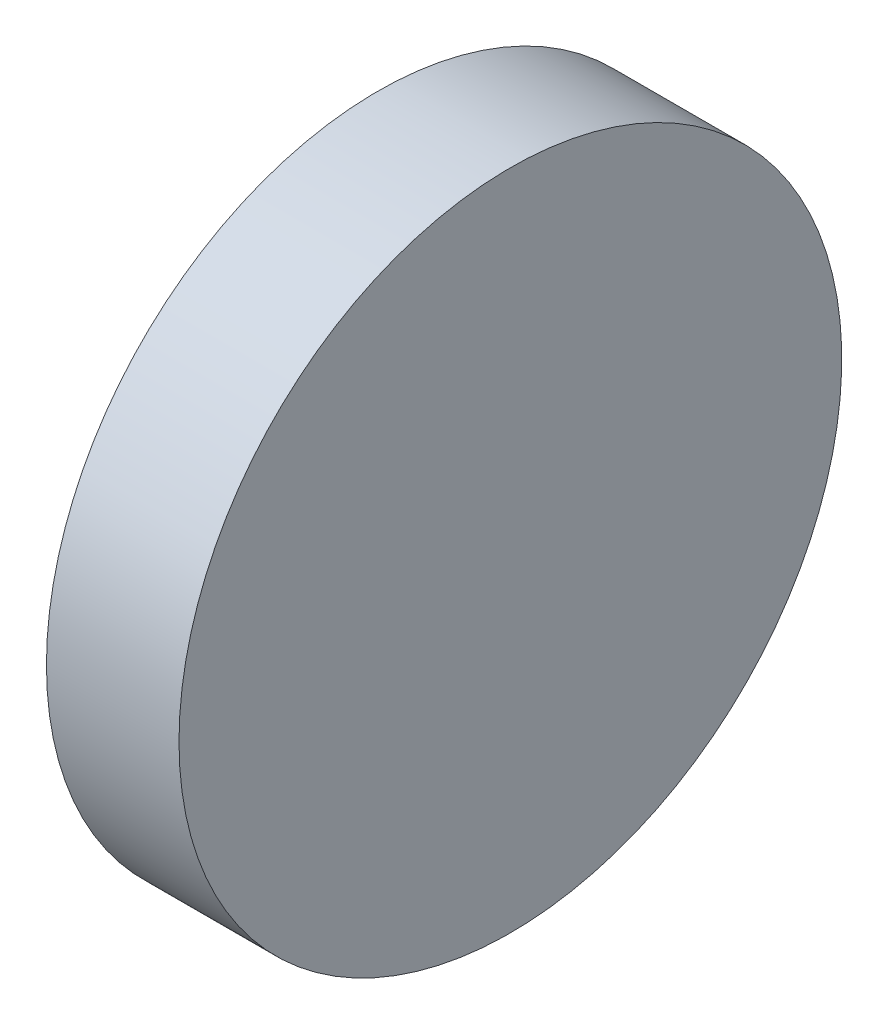
SolidWorks part; units mm, degrees
ref_plane "前视基准面" through (0, 0, 0) normal (0, 0, 1) x (1, 0, 0)
ref_plane "上视基准面" through (0, 0, 0) normal (0, 1, 0) x (1, 0, 0)
ref_plane "右视基准面" through (0, 0, 0) normal (1, 0, 0) x (0, 0, -1)
sketch "草图1" plane through (0, 0, 0) normal (0, 0, 1) x (1, 0, 0)
  line L0 (508.0016, 154.5864) -> (542.9445, 154.5864) construction
  line L1 (520.3143, 154.5864) -> (520.3143, 179.5864)
  line L2 (530.3143, 154.5864) -> (530.3143, 179.5864)
  line L3 (520.3143, 154.5864) -> (530.3143, 154.5864)
  line L5 (520.3143, 179.5864) -> (530.3143, 179.5864)
  dimension "D1" = 10
  dimension "D2" = 25
revolve "旋转1" add sketch "草图1" angle 360 about L0
